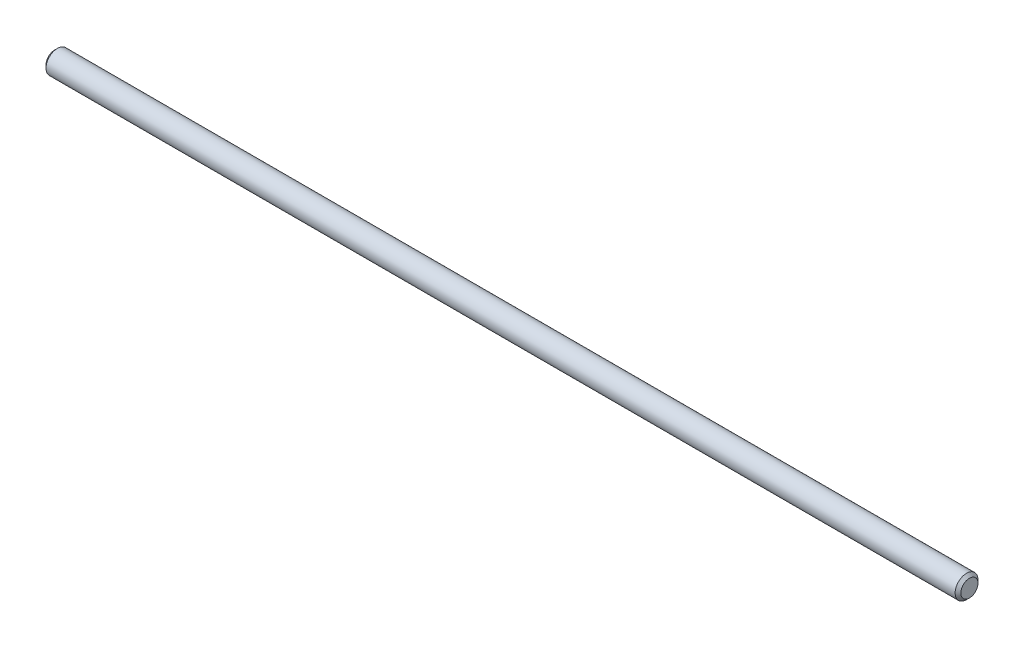
SolidWorks part; units mm, degrees
ref_plane "Front Plane" through (0, 0, 0) normal (0, 0, 1) x (1, 0, 0)
ref_plane "Top Plane" through (0, 0, 0) normal (0, 1, 0) x (1, 0, 0)
ref_plane "Right Plane" through (0, 0, 0) normal (1, 0, 0) x (0, 0, -1)
sketch "Sketch1" plane through (0, 0, 0) normal (1, 0, 0) x (0, 0, -1)
  circle A0 centre (0, 0) radius 2
  dimension "D1" = 4
extrude "Boss-Extrude1" add sketch "Sketch1" along normal mid plane 160
cosmetic thread "Cosmetic Thread2" parameters "D1"=8, "D2"=3.22
cosmetic thread "Cosmetic Thread3" parameters "D1"=8, "D2"=3.22
chamfer "Chamfer1" distance 0.5 angle 45 2 edges at (80, 0, -2) (-80, 0, -2)
